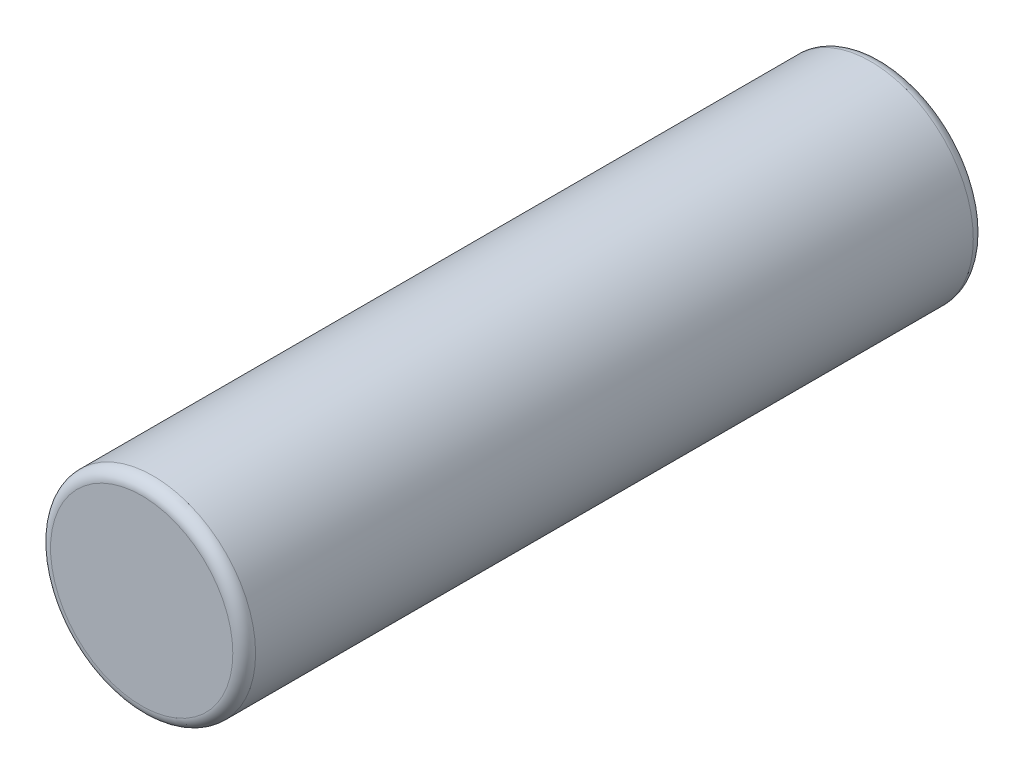
SolidWorks part; units mm, degrees
ref_plane "Ebene vorne" through (0, 0, 0) normal (0, 0, 1) x (1, 0, 0)
ref_plane "Ebene oben" through (0, 0, 0) normal (0, 1, 0) x (1, 0, 0)
ref_plane "Ebene rechts" through (0, 0, 0) normal (1, 0, 0) x (0, 0, -1)
sketch "Skizze1" plane through (0, 0, 0) normal (0, 0, 1) x (1, 0, 0)
  circle A0 centre (0, 0) radius 9
  dimension "D1" = 18
extrude "Aufsatz-Linear austragen1" add sketch "Skizze1" along normal blind 65
fillet "Verrundung1" radius 1 2 edges at (9, 0, 65) (9, 0, 0)
